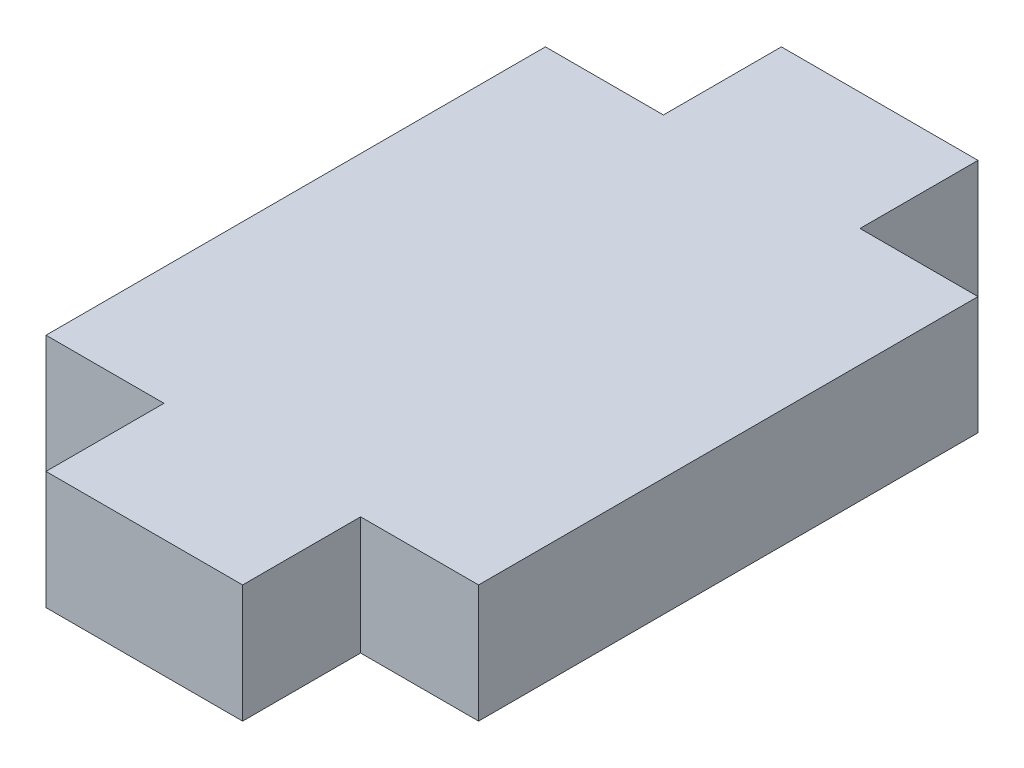
SolidWorks part; units mm, degrees
ref_plane "Front Plane" through (0, 0, 0) normal (0, 0, 1) x (1, 0, 0)
ref_plane "Top Plane" through (0, 0, 0) normal (0, 1, 0) x (1, 0, 0)
ref_plane "Right Plane" through (0, 0, 0) normal (1, 0, 0) x (0, 0, -1)
sketch "Sketch1" plane through (0, 0, 0) normal (0, 1, 0) x (1, 0, 0)
  line L0 (-5.5, 6.35) -> (-5.5, -6.35)
  line L1 (-5.5, -6.35) -> (-2.5, -6.35)
  line L2 (-2.5, -6.35) -> (-2.5, -9.35)
  line L3 (-2.5, -9.35) -> (2.5, -9.35)
  line L4 (2.5, -9.35) -> (2.5, -6.35)
  line L5 (2.5, -6.35) -> (5.5, -6.35)
  line L6 (5.5, -6.35) -> (5.5, 6.35)
  line L7 (5.5, 6.35) -> (2.5, 6.35)
  line L8 (2.5, 6.35) -> (2.5, 9.35)
  line L9 (2.5, 9.35) -> (-2.5, 9.35)
  line L10 (-2.5, 9.35) -> (-2.5, 6.35)
  line L11 (-2.5, 6.35) -> (-5.5, 6.35)
  point P2 (0, 9.35)
  point P13 (5.5, 0)
  dimension "D1" = 3
  dimension "D2" = 12.7
  dimension "D3" = 5
extrude "Boss-Extrude1" add sketch "Sketch1" along normal mid plane 3
